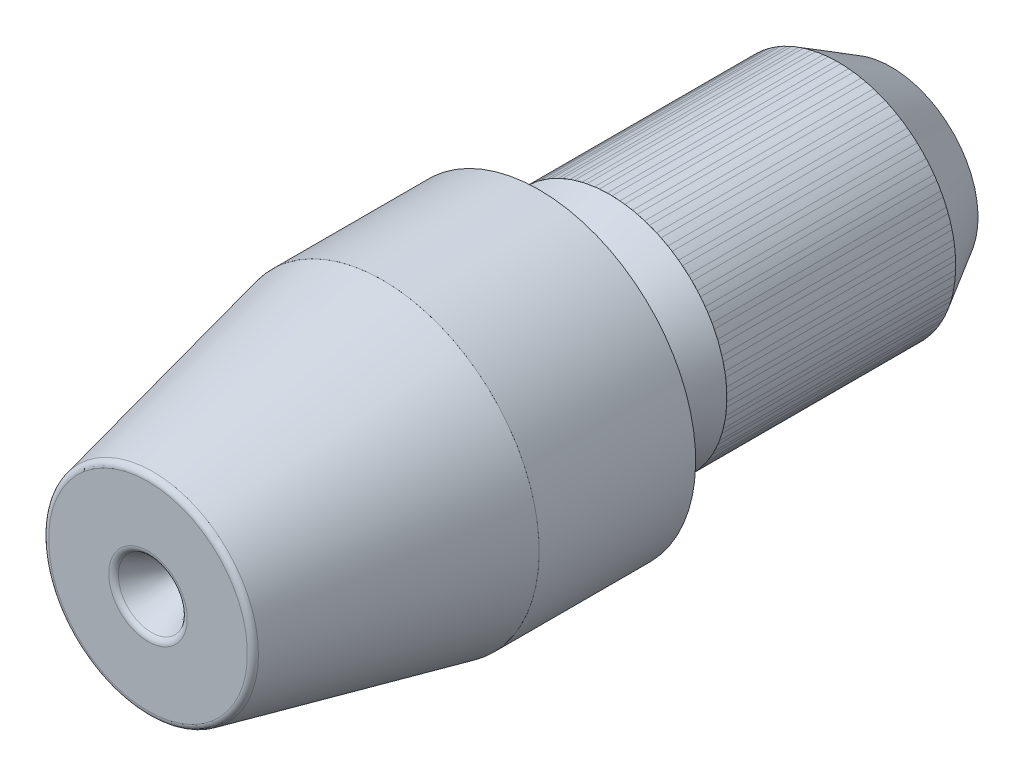
SolidWorks part; units mm, degrees
ref_plane "Front" through (0, 0, 0) normal (0, 0, 1) x (1, 0, 0)
ref_plane "Top" through (0, 0, 0) normal (0, 1, 0) x (1, 0, 0)
ref_plane "Right" through (0, 0, 0) normal (1, 0, 0) x (0, 0, -1)
sketch "Sketch1" plane through (0, 0, 0) normal (1, 0, 0) x (0, 0, -1)
  line L0 (-9.5, 0) -> (9.5, 0) construction
  line L1 (-9.5, -4) -> (-9.5, 4) construction
  line L2 (9.5, -3) -> (9.5, 3) construction
  line L3 (-9.5, 0) -> (0.5, 0) construction
  line L4 (-9.5, 0) -> (-3.5, 0) construction
  line L5 (9.5, 3) -> (0.5, 3) construction
  line L6 (-3.5, 4) -> (-9.5, 2.6698) construction
  line L7 (-3.5, 4) -> (0.5, 4) construction
  line L8 (0.5, 4) -> (0.5, 3) construction
  point P3 (0.5, -3)
  point P4 (0, 0)
  point P7 (-9.5, 0)
  point P11 (9.5, 0)
  point P14 (-3.5, 4)
  point P18 (-9.5, 2.6698)
  point P19 (0.5, 4)
  point P20 (0.5, 3)
  point P21 (0.5, -4)
  point P22 (-3.5, -4)
  point P23 (-9.5, -2.6698)
  dimension "Overall Height" = 19
  dimension "Head Diameter" = 8
  dimension "Shank Diameter" = 6
  dimension "Head Height" = 10
  dimension "Head End Height" = 6
  dimension "D1" = 12.5
  dimension "D2" = 9
sketch "Sketch2" plane through (0, 0, 0) normal (0, 0, 1) x (1, 0, 0)
  line L0 (-3.1983, 0) -> (-0.9558, 3.8841) construction
  line L1 (-3.1983, 0) -> (-0.9558, -3.8841) construction
  line L2 (0.9558, 3.8841) -> (3.1983, 0) construction
  line L3 (3.1983, 0) -> (0.9558, -3.8841) construction
  line L4 (-3.1983, 0) -> (3.1983, 0) construction
  line L5 (2.3987, 1.3849) -> (2.3121, 1.3349) construction
  line L6 (0.8228, 3.9145) -> (3.0829, 0) construction
  circle A0 centre (0, 0) radius 4 construction
  circle A1 centre (0, 0) radius 0.9 construction
  circle A2 centre (0, 0) radius 3.1983 construction
  circle A3 centre (0, 0) radius 2.6698 construction
  point P13 (0, 0)
  dimension "D2" = 1.8
  dimension "D1" = 60
  dimension "D3" = 0.1
sketch "Sketch3" plane through (0, 0, 0) normal (1, 0, 0) x (0, 0, -1)
  line L0 (-9.5, 0) -> (-9.5, 2.6698)
  line L1 (-9.5, 2.6698) -> (-3.5, 4)
  line L2 (-3.5, 4) -> (0.5, 4)
  line L3 (0.5, 4) -> (0.5, 3)
  line L4 (0.5, 3) -> (9.5, 3)
  line L5 (9.5, 3) -> (9.5, 0)
  line L6 (9.5, 0) -> (-9.5, 0)
  line L7 (9.5, 3) -> (0.5, 3) construction
revolve "Revolve2" add sketch "Sketch3" angle 360 about L6
sketch "Sketch14" plane through (0, 0, -0.5) normal (0, 0, -1) x (-1, 0, 0)
  line L0 (-3.1983, 0) -> (-0.9558, -3.8841) construction
  line L1 (-0.9558, 3.8841) -> (-3.1983, 0) construction
  line L2 (-3.1983, 0) -> (-0.9558, -3.8841)
  line L3 (-0.9558, 3.8841) -> (-3.1983, 0)
  line L5 (-6.1983, 7.7682) -> (-6.1983, -7.7682)
  line L7 (-0.9558, 3.8841) -> (1.2867, 7.7682)
  line L8 (1.2867, 7.7682) -> (-6.1983, 7.7682)
  line L9 (3.1983, 0) -> (-3.1983, 0) construction
  line L10 (-3.1983, 0) -> (-6.1983, 0) construction
  line L11 (-6.1983, -7.7682) -> (1.2867, -7.7682)
  line L12 (1.2867, -7.7682) -> (-0.9558, -3.8841)
  arc A1 (-0.9558, -3.8841) -> (-0.9558, 3.8841) centre (0, 0) ccw construction
  circle A2 centre (0, 0) radius 4 construction
  dimension "D1" = 3
sketch "Sketch16" plane through (0, 0, 0) normal (1, 0, 0) x (0, 0, -1)
  line L0 (0.5, 3) -> (0.3917, 2.8125)
  line L1 (0.5, 4) -> (0.5, 3) construction
  line L2 (0.5, 2.625) -> (1.1375, 2.625)
  line L3 (1.394, 2.6702) -> (2.3, 3)
  line L4 (9.5, 3) -> (0.5, 3) construction
  line L5 (2.3, 3) -> (0.5, 3)
  line L7 (0.5, -3) -> (0.5, 3) construction
  line L8 (9.5, -3) -> (9.5, 3) construction
  line L9 (8.15, 3) -> (9.5, 2.2206)
  line L10 (9.5, 2.2206) -> (9.5, 3)
  line L11 (9.5, 3) -> (8.15, 3)
  line L13 (0.5, -4) -> (0.5, 4) construction
  arc A0 (0.3917, 2.8125) -> (0.5, 2.625) centre (0.5, 2.75) ccw
  arc A1 (1.1375, 2.625) -> (1.394, 2.6702) centre (1.1375, 3.375) ccw
  dimension "D4" = 0.75
  dimension "D1" = 1.8
  dimension "D2" = 1.35
  dimension "D6" = 20
  dimension "D5" = 0.375
  dimension "D8" = 30
  dimension "D3" = 30
revolve "Cut-Revolve1" cut sketch "Sketch16" angle 360 about L0
sketch "Sketch10" plane through (0, 0, 9.5) normal (0, 0, 1) x (1, 0, 0)
  circle A0 centre (0, 0) radius 0.9 construction
  circle A1 centre (0, 0) radius 0.9
extrude "Cut-Extrude2" cut sketch "Sketch10" against normal blind 1.2 draft 30
sketch "Sketch15" plane through (0, 0, -9.5) normal (0, 0, -1) x (-1, 0, 0)
  circle A0 centre (0, 0) radius 0.9 construction
  circle A1 centre (0, 0) radius 0.9
extrude "Cut-Extrude5" cut sketch "Sketch15" against normal blind 1.2 draft 30
fillet "Fillet1" radius 0.16 1 edges at (0, 2.6698, 9.5)
fillet "Fillet3" radius 0.18 2 edges at (0, 0.9, -9.5) (0.9, 0, 9.5)
sketch "Sketch17" plane through (0, 0, -0.5) normal (0, 0, -1) x (-1, 0, 0)
  circle A0 centre (0, 0) radius 4 construction
  circle A1 centre (0, 0) radius 4
  circle A2 centre (0, 0) radius 4.001
  dimension "D1" = 0.001
extrude "Boss-Extrude1" add sketch "Sketch17" against normal up to vertex (4 mm away) separate body up to point (0, 4, 3.5)
ref_plane "Plane1" through (0, 0, -8.15) normal (0, 0, -1) x (-1, 0, 0)
sketch "Sketch19" plane through (0, 0, -8.15) normal (0, 0, -1) x (-1, 0, 0)
  circle A0 centre (0, 0) radius 3 construction
  circle A1 centre (0, 0) radius 3
  circle A2 centre (0, 0) radius 3.001
  dimension "D1" = 0.001
extrude "Boss-Extrude2" add sketch "Sketch19" against normal up to vertex (5.85 mm away) separate body up to point (0, 3, -2.3)
equation "\"D2@Sketch2\"=\"Shank Diameter@Sketch1\"*.3"
equation "\"D1@Fillet1\"=\"Head Diameter@Sketch1\"*.02"
equation "\"D1@Cut-Extrude2\"=\"Head Diameter@Sketch1\"*.15"
equation "\"D1@Cut-Extrude5\"=\"Head Diameter@Sketch1\"*.15"
equation "\"D1@Sketch16\"=\"D2@Sketch1\"*.2"
equation "\"D2@Sketch16\"=\"D2@Sketch1\"*.15"
equation "\"D5@Sketch16\"=\"Shank Diameter@Sketch1\"*.0625"
equation "\"D4@Sketch16\"=\"D5@Sketch16\"*2"
equation "\"D1@Fillet3\"=\"D2@Sketch2\"*.1"
equation "\"D3@Sketch2\"=\"Head Diameter@Sketch1\"*.0125"
